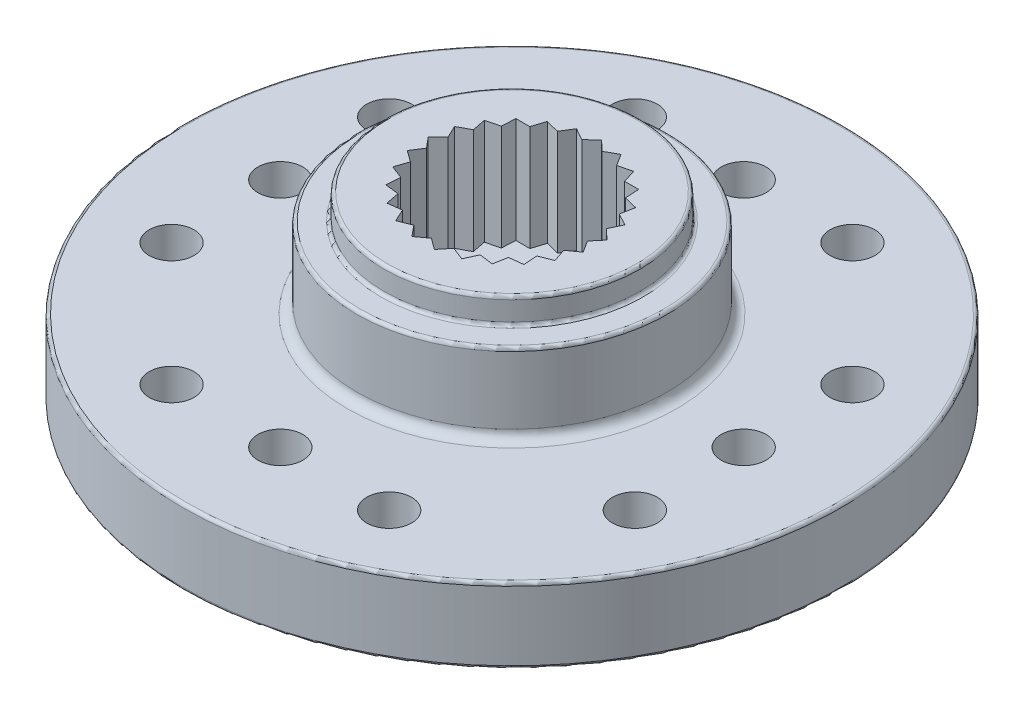
SolidWorks part; units mm, degrees
material "Custom Plastic"
ref_plane "Front Plane" through (0, 0, 0) normal (0, 0, 1) x (1, 0, 0)
ref_plane "Top Plane" through (0, 0, 0) normal (0, 1, 0) x (1, 0, 0)
ref_plane "Right Plane" through (0, 0, 0) normal (1, 0, 0) x (0, 0, -1)
sketch "Sketch1" plane through (0, 0, 0) normal (0, 1, 0) x (1, 0, 0)
  circle A0 centre (0, 0) radius 10.3
  circle A1 centre (0, 0) radius 1.39
extrude "Boss-Extrude1" add sketch "Sketch1" along normal blind 2.35
sketch "Sketch2" plane through (0, 2.35, 0) normal (0, 1, 0) x (1, 0, 0)
  line L0 (0, 0) -> (0, 2.8) construction
  line L1 (0, 0) -> (0.3509, 2.7779) construction
  line L2 (0, 0) -> (-0.3509, 2.7779) construction
  line L3 (0, 2.8) -> (-0.3158, 2.5)
  line L4 (0, 2.8) -> (0.3158, 2.5)
  line L5 (0.6963, 2.712) -> (0.3158, 2.5)
  line L6 (0.6963, 2.712) -> (0.9276, 2.3429)
  line L7 (1.3489, 2.4537) -> (0.9276, 2.3429)
  line L8 (1.3489, 2.4537) -> (1.4811, 2.0386)
  line L9 (1.9167, 2.0411) -> (1.4811, 2.0386)
  line L10 (1.9167, 2.0411) -> (1.9416, 1.6062)
  line L11 (2.3641, 1.5003) -> (1.9416, 1.6062)
  line L12 (2.3641, 1.5003) -> (2.28, 1.0729)
  line L13 (2.663, 0.8652) -> (2.28, 1.0729)
  line L14 (2.663, 0.8652) -> (2.4752, 0.4722)
  line L15 (2.7945, 0.1758) -> (2.4752, 0.4722)
  line L16 (2.7945, 0.1758) -> (2.5149, -0.1582)
  line L17 (2.7504, -0.5247) -> (2.5149, -0.1582)
  line L18 (2.7504, -0.5247) -> (2.3965, -0.7787)
  line L19 (2.5335, -1.1922) -> (2.3965, -0.7787)
  line L20 (2.5335, -1.1922) -> (2.1276, -1.3502)
  line L21 (2.1574, -1.7848) -> (2.1276, -1.3502)
  line L22 (2.1574, -1.7848) -> (1.725, -1.8369)
  line L23 (1.6458, -2.2652) -> (1.725, -1.8369)
  line L24 (1.6458, -2.2652) -> (1.214, -2.2082)
  line L25 (1.0307, -2.6034) -> (1.214, -2.2082)
  line L26 (1.0307, -2.6034) -> (0.6267, -2.4407)
  line L27 (0.3509, -2.7779) -> (0.6267, -2.4407)
  line L28 (0.3509, -2.7779) -> (0, -2.5199)
  line L29 (-0.3509, -2.7779) -> (0, -2.5199)
  line L30 (-0.3509, -2.7779) -> (-0.6267, -2.4407)
  line L31 (-1.0307, -2.6034) -> (-0.6267, -2.4407)
  line L32 (-1.0307, -2.6034) -> (-1.214, -2.2082)
  line L33 (-1.6458, -2.2652) -> (-1.214, -2.2082)
  line L34 (-1.6458, -2.2652) -> (-1.725, -1.8369)
  line L35 (-2.1574, -1.7848) -> (-1.725, -1.8369)
  line L36 (-2.1574, -1.7848) -> (-2.1276, -1.3502)
  line L37 (-2.5335, -1.1922) -> (-2.1276, -1.3502)
  line L38 (-2.5335, -1.1922) -> (-2.3965, -0.7787)
  line L39 (-2.7504, -0.5247) -> (-2.3965, -0.7787)
  line L40 (-2.7504, -0.5247) -> (-2.5149, -0.1582)
  line L41 (-2.7945, 0.1758) -> (-2.5149, -0.1582)
  line L42 (-2.7945, 0.1758) -> (-2.4752, 0.4722)
  line L43 (-2.663, 0.8652) -> (-2.4752, 0.4722)
  line L44 (-2.663, 0.8652) -> (-2.28, 1.0729)
  line L45 (-2.3641, 1.5003) -> (-2.28, 1.0729)
  line L46 (-2.3641, 1.5003) -> (-1.9416, 1.6062)
  line L47 (-1.9167, 2.0411) -> (-1.9416, 1.6062)
  line L48 (-1.9167, 2.0411) -> (-1.4811, 2.0386)
  line L49 (-1.3489, 2.4537) -> (-1.4811, 2.0386)
  line L50 (-1.3489, 2.4537) -> (-0.9276, 2.3429)
  line L51 (-0.6963, 2.712) -> (-0.9276, 2.3429)
  line L52 (-0.6963, 2.712) -> (-0.3158, 2.5)
  circle A0 centre (0, 0) radius 4.85
  circle A1 centre (0, 0) radius 2.8 construction
  point P83 (0, 0)
  dimension "D1" = 9.7
  dimension "D2" = 5.6
  dimension "D3" = 14.4
  dimension "D4" = 0.3
  dimension "D5" = 25
extrude "Boss-Extrude2" add sketch "Sketch2" along normal blind 3.3
sketch "Sketch3" plane through (0, 5.65, 0) normal (0, 1, 0) x (1, 0, 0)
  circle A0 centre (0, 0) radius 4
  circle A1 centre (0, 0) radius 4.85
extrude "Cut-Extrude1" cut sketch "Sketch3" against normal blind 0.8
sketch "Sketch4" plane through (0, 0, 0) normal (0, -1, 0) x (-1, 0, 0)
  circle A0 centre (0, 0) radius 4.4
  circle A1 centre (0, 0) radius 3.35
  circle A3 centre (0, 0) radius 2.85
  circle M2 centre (0, 0) radius 1.39
  dimension "D1" = 8.8
  dimension "D2" = 6.7
  dimension "D3" = 0.5
extrude "Cut-Extrude2" cut sketch "Sketch4" against normal blind 1.7 contours A0 A1 | A3 M2
sketch "Sketch5" plane through (0, 0, 0) normal (0, -1, 0) x (1, 0, 0)
  circle A0 centre (0, 7.24) radius 0.7
  circle A1 centre (3.4, 7.24) radius 0.7
  circle A2 centre (-3.4, 7.24) radius 0.7
  circle A5 centre (7.24, 0) radius 0.7
  circle A6 centre (7.24, -3.4) radius 0.7
  circle A7 centre (7.24, 3.4) radius 0.7
  circle A8 centre (0, -7.24) radius 0.7
  circle A9 centre (-3.4, -7.24) radius 0.7
  circle A10 centre (3.4, -7.24) radius 0.7
  circle A11 centre (-7.24, 0) radius 0.7
  circle A12 centre (-7.24, 3.4) radius 0.7
  circle A13 centre (-7.24, -3.4) radius 0.7
  point P28 (0, 0)
  dimension "D1" = 1.4
  dimension "D2" = 3.4
  dimension "D3" = 3.4
  dimension "D4" = 4
extrude "Cut-Extrude3" cut sketch "Sketch5" against normal through all
fillet "Fillet1" radius 0.1 5 edges at (0, 4.85, 4.85) (0, 4.85, 4) (0, 5.65, 4) (0, 0, 10.3) (0, 2.35, 10.3)
fillet "Fillet2" radius 0.3 1 edges at (0, 2.35, 4.85)
